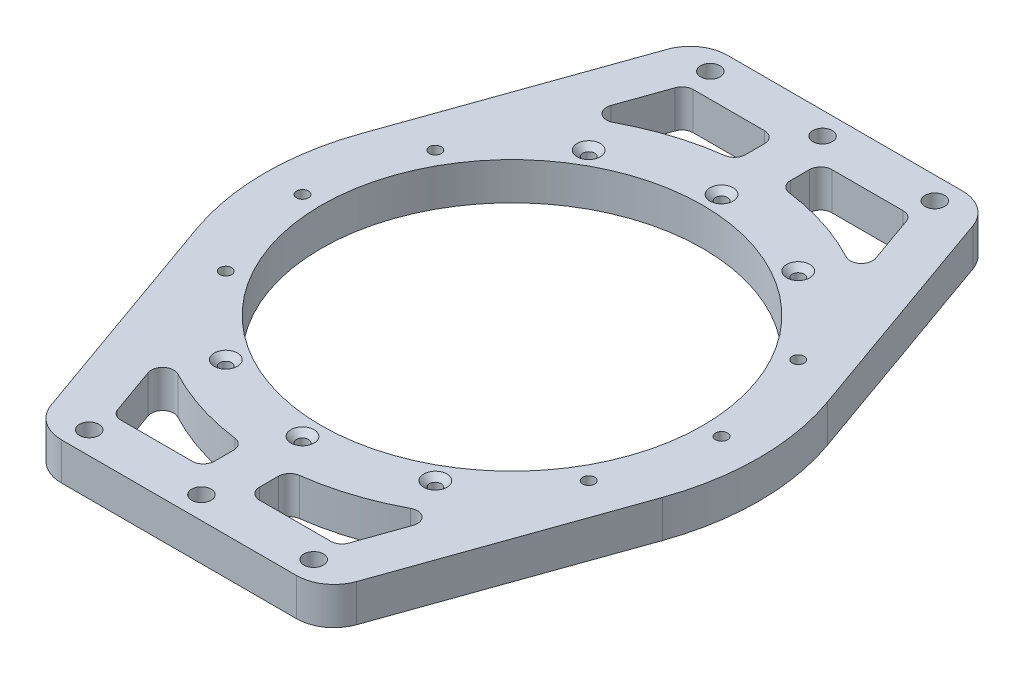
SolidWorks part; units mm, degrees
material "Thornel Mat VMA1"
ref_plane "前视基准面" through (0, 0, 0) normal (0, 0, 1) x (1, 0, 0)
ref_plane "上视基准面" through (0, 0, 0) normal (0, 1, 0) x (1, 0, 0)
ref_plane "右视基准面" through (0, 0, 0) normal (1, 0, 0) x (0, 0, -1)
sketch "草图1" plane through (0, 0, 0) normal (0, 1, 0) x (1, 0, 0)
  line L0 (0, 90) -> (0, 75) construction
  line L1 (-120, 90) -> (120, 90)
  line L2 (-120, 90) -> (-120, -90)
  line L3 (-120, -90) -> (120, -90)
  line L4 (120, 90) -> (120, -90)
  line L5 (0, -90) -> (0, 90) construction
  line L6 (-120, 0) -> (120, 0) construction
  line L7 (0, 75) -> (-60, 75) construction
  line L8 (120, 0) -> (112, 0) construction
  line L9 (0, 0) -> (0, 56) construction
  line L10 (0, 0) -> (0, 56) construction
  line L11 (0, 0) -> (28, 48.4974) construction
  line L12 (-70, 85) -> (-50, 85) construction
  line L13 (-70, 85) -> (-70, 65) construction
  line L14 (-70, 65) -> (-50, 65) construction
  line L15 (-50, 85) -> (-50, 65) construction
  line L16 (-60, 65) -> (-60, 85) construction
  line L17 (-70, 75) -> (-50, 75) construction
  line L18 (112, 0) -> (112, 10) construction
  line L19 (112, 10) -> (112, 30) construction
  circle A8 centre (0, 0) radius 51
  circle A9 centre (0, 56) radius 1.6
  circle A10 centre (28, 48.4974) radius 1.6
  circle A11 centre (48.4974, 28) radius 1.6
  circle A12 centre (56, 0) radius 1.6
  circle A13 centre (48.4974, -28) radius 1.6
  circle A14 centre (28, -48.4974) radius 1.6
  circle A15 centre (0, -56) radius 1.6
  circle A16 centre (-28, -48.4974) radius 1.6
  circle A17 centre (-48.4974, -28) radius 1.6
  circle A18 centre (-56, 0) radius 1.6
  circle A19 centre (-48.4974, 28) radius 1.6
  circle A20 centre (-28, 48.4974) radius 1.6
  circle A21 centre (-70, 85) radius 2.1
  circle A22 centre (-50, 85) radius 2.1
  circle A23 centre (-70, 65) radius 2.1
  circle A24 centre (-50, 65) radius 2.1
  circle A25 centre (50, 85) radius 2.1
  circle A26 centre (50, 65) radius 2.1
  circle A27 centre (70, 65) radius 2.1
  circle A28 centre (70, 85) radius 2.1
  circle A29 centre (70, -85) radius 2.1
  circle A30 centre (70, -65) radius 2.1
  circle A31 centre (50, -65) radius 2.1
  circle A32 centre (50, -85) radius 2.1
  circle A33 centre (-50, -65) radius 2.1
  circle A34 centre (-70, -65) radius 2.1
  circle A35 centre (-50, -85) radius 2.1
  circle A36 centre (-70, -85) radius 2.1
  circle A45 centre (112, 10) radius 1.25
  circle A46 centre (112, 30) radius 1.25
  circle A47 centre (112, -30) radius 1.25
  circle A48 centre (112, -10) radius 1.25
  circle A49 centre (-112, -30) radius 1.25
  circle A50 centre (-112, -10) radius 1.25
  circle A51 centre (-112, 30) radius 1.25
  circle A52 centre (-112, 10) radius 1.25
  point P0 (0, 0)
  dimension "D6" = 4.2
  dimension "D7" = 4.2
  dimension "D8" = 102
  dimension "D10" = 3.2
  dimension "D14" = 4.2
  dimension "D15" = 4.2
  dimension "D19" = 2.5
  dimension "D20" = 2.5
  dimension "D1" = 180
  dimension "D2" = 240
  dimension "D3" = 15
  dimension "D4" = 60
  dimension "D5" = 20
  dimension "D9" = 56
  dimension "D12" = 56
  dimension "D13" = 30
  dimension "D16" = 8
  dimension "D17" = 10
  dimension "D18" = 20
  dimension "D11" = 12
extrude "凸台-拉伸1" add sketch "草图1" along normal blind 10
sketch "草图2" plane through (0, 10, 0) normal (0, 1, 0) x (1, 0, 0)
  line L0 (-120, 57.5) -> (-110, 47.5)
  line L1 (-120, 90) -> (-120, -90) construction
  line L2 (-110, 47.5) -> (-110, -47.5)
  line L3 (-110, -47.5) -> (-120, -57.5)
  line L4 (-120, -57.5) -> (-120, 57.5)
  line L5 (0, 0) -> (0, 90) construction
  line L6 (120, 90) -> (-120, 90) construction
  line L7 (-110, 0) -> (-120, 0) construction
  line L8 (110, -47.5) -> (120, -57.5)
  line L9 (110, 47.5) -> (110, -47.5)
  line L10 (120, 57.5) -> (110, 47.5)
  line L11 (120, -57.5) -> (120, 57.5)
  dimension "D1" = 95
  dimension "D2" = 10
extrude "切除-拉伸1" cut sketch "草图2" against normal through all
sketch "草图3" plane through (0, 10, 0) normal (0, 1, 0) x (1, 0, 0)
  line L2 (120, 57.5) -> (120, 90) construction
  line L3 (0, 0) -> (0, 90) construction
  line L4 (120, 90) -> (-120, 90) construction
  line L5 (0, 0) -> (-110, 0) construction
  line L6 (-110, -47.5) -> (-110, 47.5) construction
  line L7 (-30, 83) -> (0, 83) construction
  line L8 (120, -90) -> (120, -57.5) construction
  line L9 (-120, 90) -> (120, 90)
  line L10 (-120, 90) -> (-120, 89)
  line L11 (-120, 89) -> (120, 89)
  line L12 (120, 90) -> (120, 89)
  line L13 (0, 89) -> (0, 90) construction
  line L14 (-120, 89.5) -> (120, 89.5) construction
  line L15 (-120, -90) -> (120, -90)
  line L16 (-120, -90) -> (-120, -89)
  line L17 (-120, -89) -> (120, -89)
  line L18 (120, -90) -> (120, -89)
  line L19 (0, -89) -> (0, -90) construction
  line L20 (-120, -89.5) -> (120, -89.5) construction
  circle A0 centre (-30, 83) radius 2.6
  circle A1 centre (0, 83) radius 2.6
  circle A2 centre (30, 83) radius 2.6
  circle A3 centre (30, -83) radius 2.6
  circle A4 centre (0, -83) radius 2.6
  circle A5 centre (-30, -83) radius 2.6
  point P167 (0, -89.5)
  point P339 (0, 89.5)
  dimension "D2" = 5.2
  dimension "D3" = 6
  dimension "D1" = 83
  dimension "D5" = 30
  dimension "D4" = 3
extrude "切除-拉伸2" cut sketch "草图3" against normal through all
sketch "草图4" plane through (0, 10, 0) normal (0, 1, 0) x (1, 0, 0)
  line L0 (0, 0) -> (0, 89) construction
  line L1 (-120, 89) -> (120, 89) construction
  line L2 (-38.4831, 89) -> (-62.2096, 22.0447)
  line L3 (-62.2096, -22.0447) -> (-38.4831, -89)
  line L4 (120, -89) -> (-120, -89) construction
  line L5 (-38.4831, -89) -> (-120, -89)
  line L6 (-120, -89) -> (-120, 89)
  line L7 (-120, 89) -> (-38.4831, 89)
  line L8 (120, -89) -> (120, 89)
  line L9 (38.4831, -89) -> (120, -89)
  line L10 (62.2096, -22.0447) -> (38.4831, -89)
  line L11 (38.4831, 89) -> (62.2096, 22.0447)
  line L12 (120, 89) -> (38.4831, 89)
  arc A0 (-62.2096, 22.0447) -> (-62.2096, -22.0447) centre (0, 0) ccw
  circle A1 centre (0, 0) radius 51 construction
  circle A2 centre (-30, 83) radius 2.6 construction
  arc A3 (62.2096, 22.0447) -> (62.2096, -22.0447) centre (0, 0) cw
  dimension "D1" = 15
  dimension "D2" = 10
extrude "切除-拉伸3" cut sketch "草图4" against normal through all
fillet "圆角1" radius 10 4 edges at (38.4831, 5, 89) (-38.4831, 5, 89) (38.4831, 5, -89) (-38.4831, 5, -89)
sketch "草图5" plane through (0, 10, 0) normal (0, 1, 0) x (1, 0, 0)
  circle A0 centre (0, 0) radius 107.5
  dimension "D1" = 215
extrude "凸台-拉伸2" [suppressed] add sketch "草图5" along normal blind 345
sketch "草图6" plane through (0, 10, 0) normal (0, 1, 0) x (1, 0, 0)
  circle A0 centre (0, 0) radius 51 construction
  circle A1 centre (0, 0) radius 51
sketch "草图7" plane through (0, 10, 0) normal (0, 1, 0) x (1, 0, 0)
  line L0 (0, 0) -> (66, 0) construction
  line L1 (0, 0) -> (0, 83) construction
  line L2 (-9, 76.5) -> (-28.0618, 76.5)
  line L3 (-30.8895, 74.502) -> (-35.3753, 61.8433)
  line L4 (-6, 73.5) -> (-6, 68.4105)
  line L5 (-62.2096, 22.0447) -> (-40.8431, 82.3401) construction
  line L6 (-31.4175, 89) -> (31.4175, 89) construction
  line L7 (9, 76.5) -> (28.0618, 76.5)
  line L8 (6, 73.5) -> (6, 68.4105)
  line L9 (30.8895, 74.502) -> (35.3753, 61.8433)
  line L10 (6, -73.5) -> (6, -68.4105)
  line L11 (30.8895, -74.502) -> (35.3753, -61.8433)
  line L12 (9, -76.5) -> (28.0618, -76.5)
  line L13 (-9, -76.5) -> (-28.0618, -76.5)
  line L14 (-6, -73.5) -> (-6, -68.4105)
  line L15 (-30.8895, -74.502) -> (-35.3753, -61.8433)
  arc A0 (62.2096, -22.0447) -> (62.2096, 22.0447) centre (0, 0) ccw construction
  arc A1 (-8.6087, 65.4362) -> (-31.1325, 58.196) centre (0, 0) ccw
  circle A2 centre (0, 0) radius 51 construction
  arc A3 (-9, 76.5) -> (-6, 73.5) centre (-9, 73.5) cw
  arc A4 (-6, 68.4105) -> (-8.6087, 65.4362) centre (-9, 68.4105) cw
  arc A5 (-35.3753, 61.8433) -> (-31.1325, 58.196) centre (-32.5476, 60.8412) ccw
  arc A6 (-28.0618, 76.5) -> (-30.8895, 74.502) centre (-28.0618, 73.5) ccw
  arc A7 (9, 76.5) -> (6, 73.5) centre (9, 73.5) ccw
  arc A8 (6, 68.4105) -> (8.6087, 65.4362) centre (9, 68.4105) ccw
  arc A9 (8.6087, 65.4362) -> (31.1325, 58.196) centre (0, 0) cw
  arc A10 (35.3753, 61.8433) -> (31.1325, 58.196) centre (32.5476, 60.8412) cw
  arc A11 (28.0618, 76.5) -> (30.8895, 74.502) centre (28.0618, 73.5) cw
  arc A12 (9, -76.5) -> (6, -73.5) centre (9, -73.5) cw
  arc A13 (6, -68.4105) -> (8.6087, -65.4362) centre (9, -68.4105) cw
  arc A14 (8.6087, -65.4362) -> (31.1325, -58.196) centre (0, 0) ccw
  arc A15 (35.3753, -61.8433) -> (31.1325, -58.196) centre (32.5476, -60.8412) ccw
  arc A16 (28.0618, -76.5) -> (30.8895, -74.502) centre (28.0618, -73.5) ccw
  arc A17 (-9, -76.5) -> (-6, -73.5) centre (-9, -73.5) ccw
  arc A18 (-6, -68.4105) -> (-8.6087, -65.4362) centre (-9, -68.4105) ccw
  arc A19 (-8.6087, -65.4362) -> (-31.1325, -58.196) centre (0, 0) cw
  arc A20 (-35.3753, -61.8433) -> (-31.1325, -58.196) centre (-32.5476, -60.8412) cw
  arc A21 (-28.0618, -76.5) -> (-30.8895, -74.502) centre (-28.0618, -73.5) cw
  dimension "D4" = 15
  dimension "D5" = 3
  dimension "D1" = 6
  dimension "D2" = 12.5
  dimension "D3" = 12
extrude "切除-拉伸4" cut sketch "草图7" against normal through all
chamfer "倒角1" distance 1.5 angle 45 6 edges at (28, 10, 50.0974) (0, 10, 57.6) (-28, 10, 50.0974) (28, 10, -46.8974) (0, 10, -54.4) (-28, 10, -46.8974)
